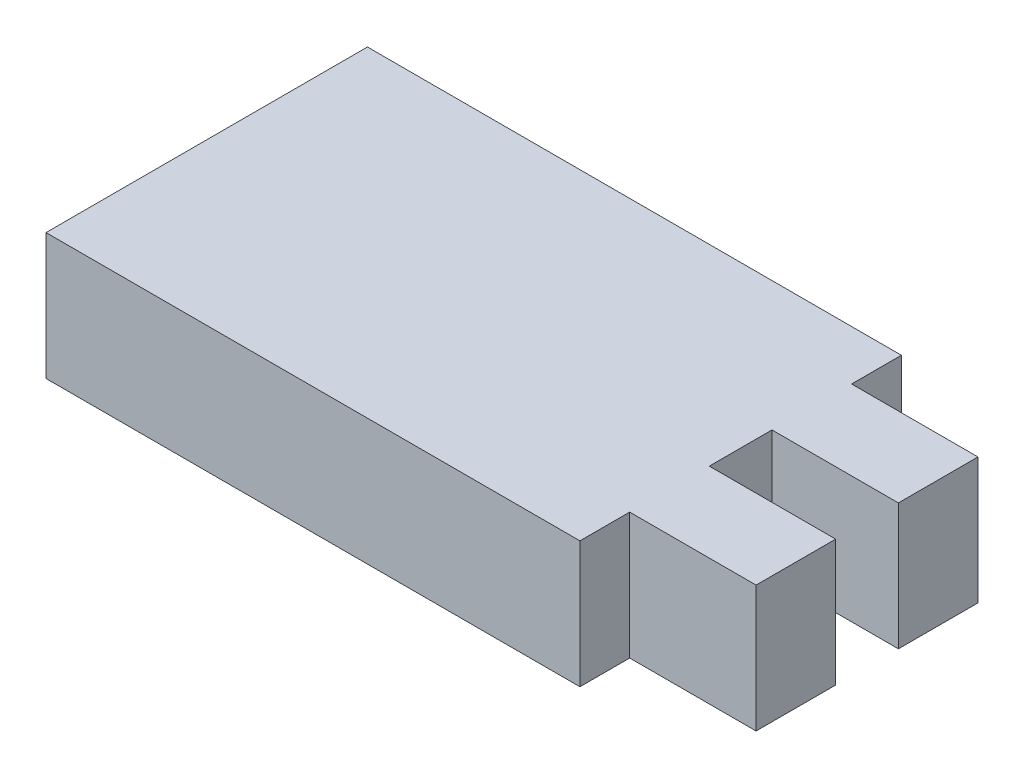
SolidWorks part; units mm, degrees
ref_plane "Front Plane" through (0, 0, 0) normal (0, 0, 1) x (1, 0, 0)
ref_plane "Top Plane" through (0, 0, 0) normal (0, 1, 0) x (1, 0, 0)
ref_plane "Right Plane" through (0, 0, 0) normal (1, 0, 0) x (0, 0, -1)
sketch "Sketch1" plane through (0, 0, 0) normal (0, 1, 0) x (1, 0, 0)
  line L0 (16.5875, 5.575) -> (10.2375, 5.575)
  line L1 (-16.5875, 8.075) -> (16.5875, 8.075) construction
  line L2 (-16.5875, 8.075) -> (-16.5875, -8.075)
  line L3 (-16.5875, -8.075) -> (16.5875, -8.075) construction
  line L4 (16.5875, 8.075) -> (16.5875, -8.075) construction
  line L5 (-16.5875, 8.075) -> (16.5875, -8.075) construction
  line L6 (-16.5875, -8.075) -> (16.5875, 8.075) construction
  line L7 (16.5875, 5.575) -> (16.5875, 1.575)
  line L8 (16.5875, 1.575) -> (10.2375, 1.575)
  line L9 (10.2375, 5.575) -> (10.2375, 8.075)
  line L12 (-16.5875, 8.075) -> (10.2375, 8.075)
  line L13 (-16.5875, -8.075) -> (10.2375, -8.075)
  line L14 (10.2375, -8.075) -> (10.2375, -5.575)
  line L15 (10.2375, -5.575) -> (16.5875, -5.575)
  line L16 (16.5875, -5.575) -> (16.5875, -1.575)
  line L17 (16.5875, -1.575) -> (10.2375, -1.575)
  line L18 (10.2375, -1.575) -> (10.2375, 1.575)
  point P0 (0, 0)
  dimension "D1" = 16.15
  dimension "D2" = 26.825
  dimension "D3" = 6.35
  dimension "D4" = 4
  dimension "D5" = 2.5
  dimension "D6" = 2.5
  dimension "D7" = 4
  dimension "D8" = 6.35
extrude "Boss-Extrude1" add sketch "Sketch1" along normal blind 6.35
